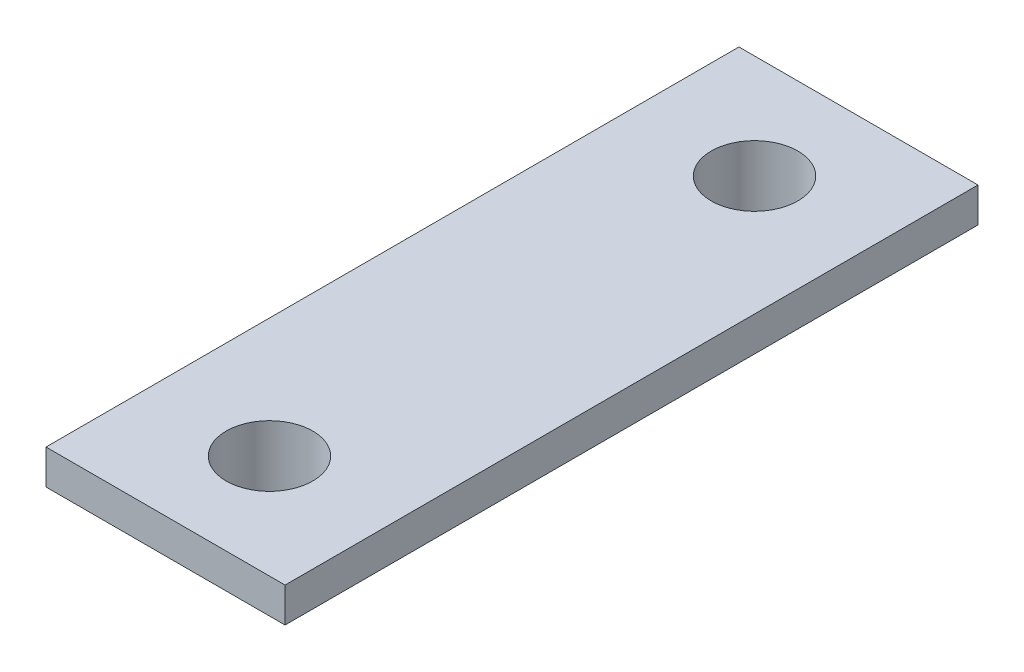
SolidWorks part; units mm, degrees
material "6061 Alloy"
ref_plane "Front Plane" through (0, 0, 0) normal (0, 0, 1) x (1, 0, 0)
ref_plane "Top Plane" through (0, 0, 0) normal (0, 1, 0) x (1, 0, 0)
ref_plane "Right Plane" through (0, 0, 0) normal (1, 0, 0) x (0, 0, -1)
sketch "Sketch1" plane through (0, 0, 0) normal (0, 1, 0) x (1, 0, 0)
  line L1 (-3.45, 10) -> (3.45, 10)
  line L2 (-3.45, 10) -> (-3.45, -10)
  line L3 (-3.45, -10) -> (3.45, -10)
  line L4 (3.45, 10) -> (3.45, -10)
  line L5 (-3.45, 10) -> (3.45, -10) construction
  line L6 (-3.45, -10) -> (3.45, 10) construction
  point P0 (0, 0)
  dimension "D1" = 20
  dimension "D2" = 6.9
extrude "Boss-Extrude1" add sketch "Sketch1" along normal blind 1
sketch "Sketch4" plane through (0, 0, 0) normal (0, -1, 0) x (1, 0, 0)
  line L0 (0, 0) -> (0, -7) construction
  circle A0 centre (0, -7) radius 1.9
  dimension "D1" = 3.8
  dimension "D2" = 7
extrude "Boss-Extrude2" add sketch "Sketch4" along normal blind 0.8
mirror "Mirror2" about plane through (0, 0, 0) normal (0, 0, 1) of "Boss-Extrude2"
hole_wizard "M3x0.5 Tapped Hole1" positions "Sketch2" profile "Sketch3" tap size "M3x0.5" standard "ANSI Metric" end condition through all
sketch "Sketch2" plane through (0, 1, 0) normal (0, 1, 0) x (1, 0, 0)
  point P0 (0, 7)
sketch "Sketch3" plane through (0, 1, -7) normal (1, 0, 0) x (0, 0, 1)
  line L0 (0, 0) -> (0, 1.8)
  line L1 (0, 1.8) -> (1.25, 1.8)
  line L2 (1.25, 1.8) -> (1.25, 0)
  line L5 (1.25, 0) -> (0, 0)
  line L11 (0, -6.35) -> (0, 107.95) construction
  dimension "Thru Tap Drill Dia." = 2.5
  dimension "Thru Tap Drill Depth" = 1.8
cosmetic thread "Hole Thread1" parameters "D2"=3
mirror "Mirror1" about plane through (0, 0, 0) normal (0, 0, 1) of "M3x0.5 Tapped Hole1"
